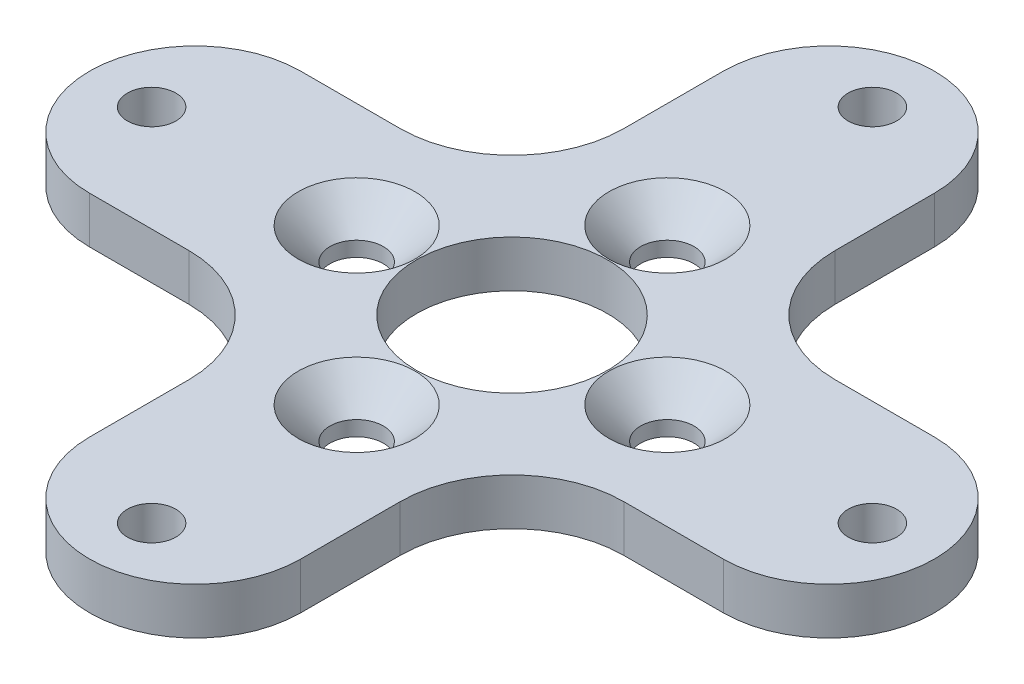
SolidWorks part; units mm, degrees
material "AISI 1015 Steel, Cold Drawn (SS)"
ref_plane "Front Plane" through (0, 0, 0) normal (0, 0, 1) x (1, 0, 0)
ref_plane "Top Plane" through (0, 0, 0) normal (0, 1, 0) x (1, 0, 0)
ref_plane "Right Plane" through (0, 0, 0) normal (1, 0, 0) x (0, 0, -1)
sketch "Sketch1" plane through (0, 0, 0) normal (0, 1, 0) x (1, 0, 0)
  line L0 (-34, 0) -> (34, 0) construction
  line L1 (0, 34) -> (0, -34) construction
  line L2 (-8.5, 25.5) -> (-8.5, 8.5)
  line L3 (8.5, 25.5) -> (8.5, 8.5)
  line L4 (-25.5, -8.5) -> (-8.5, -8.5)
  line L5 (-25.5, 8.5) -> (-8.5, 8.5)
  line L6 (8.5, 8.5) -> (25.5, 8.5)
  line L7 (-34, 8.5) -> (34, 8.5) construction
  line L8 (-8.5, -8.5) -> (-8.5, -25.5)
  line L9 (-8.5, 34) -> (-8.5, -34) construction
  line L10 (8.5, -8.5) -> (25.5, -8.5)
  line L11 (-34, -8.5) -> (34, -8.5) construction
  line L12 (8.5, -8.5) -> (8.5, -25.5)
  line L13 (8.5, 34) -> (8.5, -34) construction
  circle A0 centre (0, 0) radius 7.7
  arc A1 (25.5, -8.5) -> (25.5, 8.5) centre (25.5, 0) ccw
  arc A2 (8.5, 25.5) -> (-8.5, 25.5) centre (0, 25.5) ccw
  arc A3 (-25.5, 8.5) -> (-25.5, -8.5) centre (-25.5, 0) ccw
  arc A4 (-8.5, -25.5) -> (8.5, -25.5) centre (0, -25.5) ccw
  circle A5 centre (0, 29) radius 1.95
  circle A6 centre (29, 0) radius 1.95
  circle A7 centre (0, -29) radius 1.95
  circle A8 centre (-29, 0) radius 1.95
  point P42 (0, 0)
  dimension "D1" = 15.4
  dimension "D7" = 3.9
  dimension "D2" = 68
  dimension "D8" = 5
  dimension "D3" = 8.5
  dimension "D4" = 8.5
  dimension "D5" = 8.5
  dimension "D6" = 8.5
  dimension "D9" = 4
extrude "Boss-Extrude1" add sketch "Sketch1" along normal blind 3.75
fillet "Fillet1" radius 9 4 edges at (-8.5, 1.875, 8.5) (8.5, 1.875, 8.5) (8.5, 1.875, -8.5) (-8.5, 1.875, -8.5)
hole_wizard "CSK for M4 Flat Head Machine Screw1" positions "Sketch2" profile "Sketch3" countersink size "M4" standard "ANSI Metric" end condition through all
sketch "Sketch2" plane through (0, 3.75, 0) normal (0, 1, 0) x (1, 0, 0)
  line L0 (0, 12.5) -> (0, 0)
  line L1 (0, 0) -> (0, -12.5)
  line L3 (12.5, 0) -> (0, 0)
  line L5 (-12.5, 0) -> (0, 0)
  point P0 (12.5, 0)
  point P2 (0, 12.5)
  point P4 (0, -12.5)
  point P6 (-12.5, 0)
  dimension "D1" = 12.5
sketch "Sketch3" plane through (12.5, 3.75, 0) normal (1, 0, 0) x (0, 0, 1)
  line L0 (0, 0) -> (0, 3.75)
  line L1 (0, 3.75) -> (2.15, 3.75)
  line L2 (2.15, 3.75) -> (2.15, 2.55)
  line L3 (2.15, 2.55) -> (4.7, 0)
  line L5 (4.7, 0) -> (0, 0)
  line L6 (-2.15, 2.55) -> (-4.7, 0) construction
  line L11 (0, -6.35) -> (0, 107.95) construction
  dimension "Thru Hole Dia." = 4.3
  dimension "Thru Hole Depth" = 3.75
  dimension "Near C'Sink Dia." = 9.4
  dimension "Near C'Sink Angle" = 90
